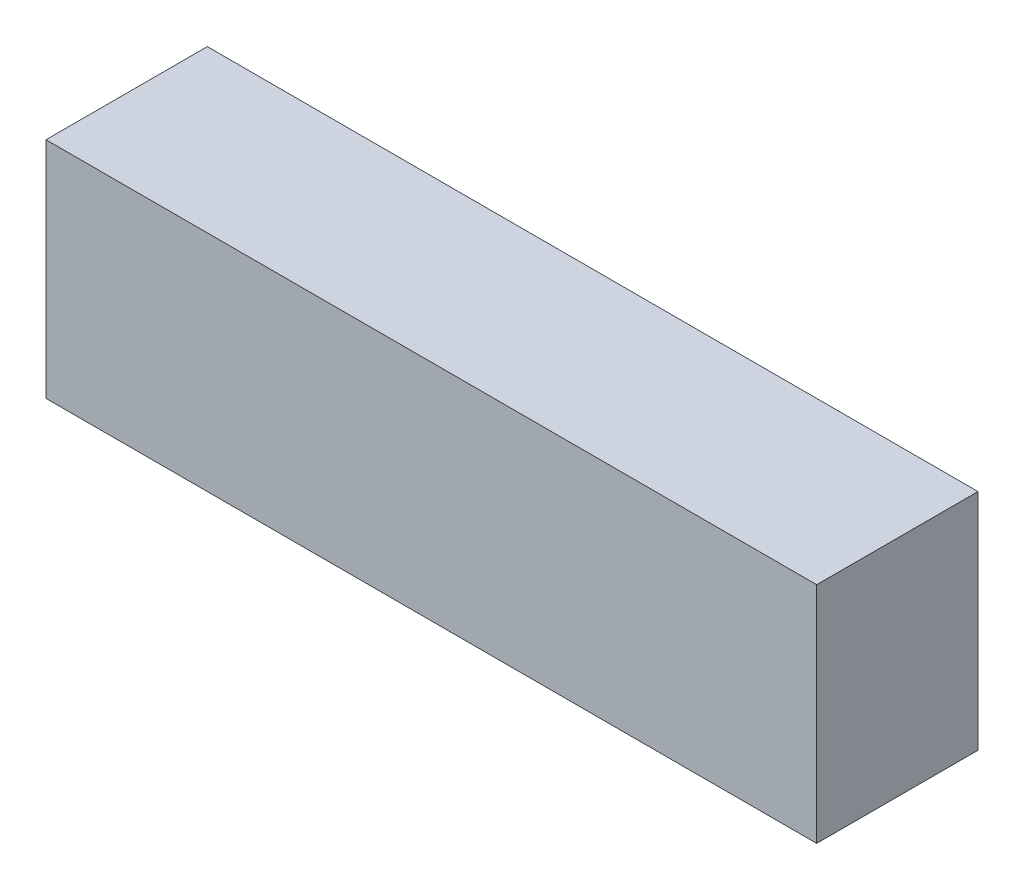
SolidWorks part; units mm, degrees
ref_plane "Front Plane" through (0, 0, 0) normal (0, 0, 1) x (1, 0, 0)
ref_plane "Top Plane" through (0, 0, 0) normal (0, 1, 0) x (1, 0, 0)
ref_plane "Right Plane" through (0, 0, 0) normal (1, 0, 0) x (0, 0, -1)
sketch "Sketch1" plane through (169.4939, 0, 0) normal (0, 0, 1) x (1, 0, 0)
  line L1 (-147.9939, 6.25) -> (-190.9939, 6.25)
  line L2 (-147.9939, 6.25) -> (-147.9939, -6.25)
  line L3 (-147.9939, -6.25) -> (-190.9939, -6.25)
  line L4 (-190.9939, 6.25) -> (-190.9939, -6.25)
  line L5 (-147.9939, 6.25) -> (-190.9939, -6.25) construction
  line L6 (-147.9939, -6.25) -> (-190.9939, 6.25) construction
  point P0 (-169.4939, 0)
  point P5 (-171.2062, 24.3798)
  point P6 (-86.2682, 20.3776)
  point P7 (0, 0)
  point P8 (0, 0)
  dimension "D1" = 12.5
  dimension "D2" = 43
extrude "Boss-Extrude1" add sketch "Sketch1" along normal blind 9 contours L3 L4 L1 L2
